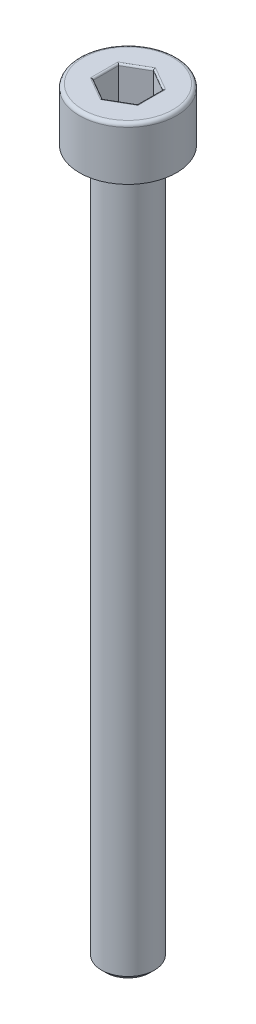
SolidWorks part; units mm, degrees
ref_plane "Front Plane" through (0, 0, 0) normal (0, 0, 1) x (1, 0, 0)
ref_plane "Top Plane" through (0, 0, 0) normal (0, 1, 0) x (1, 0, 0)
ref_plane "Right Plane" through (0, 0, 0) normal (1, 0, 0) x (0, 0, -1)
sketch "Sketch1" plane through (0, 0, 0) normal (0, 0, 1) x (1, 0, 0)
  line L0 (0, 0) -> (0, -47.0967) construction
  line L1 (0, -43) -> (-1.5, -43)
  line L2 (-1.5, -43) -> (-1.5, -3)
  line L3 (-1.5, -3) -> (-2.75, -3)
  line L4 (-2.75, -3) -> (-2.75, 0)
  line L5 (-2.75, 0) -> (0, 0)
  line L6 (0, 0) -> (0, -43)
  dimension "D1" = 40
  dimension "d" = 3
  dimension "k" = 3
  dimension "dk" = 5.5
revolve "Revolve1" add sketch "Sketch1" angle 360 about L0
chamfer "Chamfer1" distance 0.25 angle 45 2 edges at (0, -3, 1.5) (0, -43, 1.5)
fillet "Fillet1" radius 0.2 1 edges at (0, 0, 2.75)
sketch "Sketch2" plane through (0, 0, 0) normal (0, 1, 0) x (1, 0, 0)
  line L1 (0, 1.4434) -> (-1.25, 0.7217)
  line L2 (-1.25, 0.7217) -> (-1.25, -0.7217)
  line L3 (-1.25, -0.7217) -> (0, -1.4434)
  line L4 (0, -1.4434) -> (1.25, -0.7217)
  line L5 (1.25, -0.7217) -> (1.25, 0.7217)
  line L6 (1.25, 0.7217) -> (0, 1.4434)
  circle A0 centre (0, 0) radius 1.25 construction
  dimension "s" = 2.5
extrude "Cut-Extrude1" cut sketch "Sketch2" against normal blind 2
fillet "Fillet2" radius 0.1 12 edges at (-0.625, 0, -1.0825) (-1.25, 0, 0) (-0.625, 0, 1.0825) (0.625, 0, 1.0825) (1.25, 0, 0) (0.625, 0, -1.0825) (1.25, -2, 0) (0.625, -2, 1.0825) (-0.625, -2, 1.0825) (-1.25, -2, 0) (-0.625, -2, -1.0825) (0.625, -2, -1.0825)
